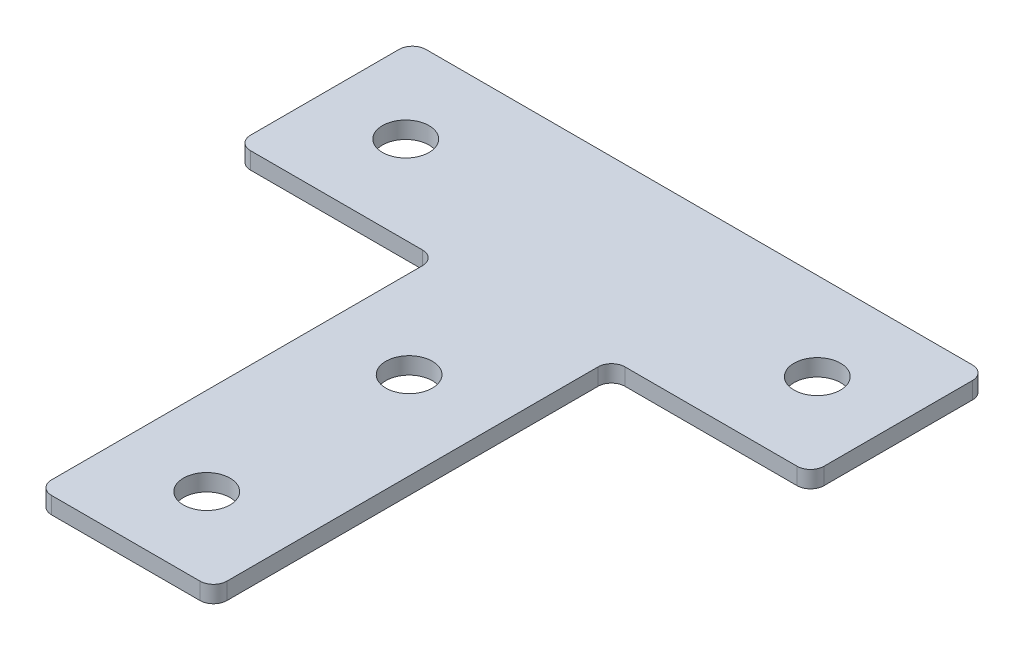
SolidWorks part; units mm, degrees
material "201 退火不锈钢 (SS)"
ref_plane "前视基准面" through (0, 0, 0) normal (0, 0, 1) x (1, 0, 0)
ref_plane "上视基准面" through (0, 0, 0) normal (0, 1, 0) x (1, 0, 0)
ref_plane "右视基准面" through (0, 0, 0) normal (1, 0, 0) x (0, 0, -1)
sketch "草图1" plane through (0, 0, 0) normal (0, 1, 0) x (1, 0, 0)
  line L0 (13, -13) -> (42.5, -13)
  line L1 (-42.5, 13) -> (42.5, 13)
  line L2 (-42.5, 13) -> (-42.5, -13)
  line L3 (-42.5, -13) -> (-13, -13)
  line L4 (42.5, 13) -> (42.5, -13)
  line L5 (-42.5, 13) -> (42.5, -13) construction
  line L6 (-42.5, -13) -> (42.5, 13) construction
  line L7 (-13, -72) -> (13, -72)
  line L8 (-13, -72) -> (-13, -13)
  line L10 (13, -72) -> (13, -13)
  line L11 (-13, -72) -> (13, -13) construction
  line L12 (-13, -13) -> (13, -72) construction
  circle A0 centre (0, -60) radius 3.45
  circle A1 centre (0, -30) radius 3.45
  circle A2 centre (-30.5, 0) radius 3.45
  circle A3 centre (30.5, 0) radius 3.45
  point P0 (0, 0)
  point P6 (0, -42.5)
  dimension "D6" = 6.9
  dimension "D7" = 12
  dimension "D8" = 30
  dimension "D9" = 12
  dimension "D10" = 12
  dimension "D1" = 85
  dimension "D2" = 85
  dimension "D3" = 26
  dimension "D4" = 26
  dimension "D5" = 0
extrude "凸台-拉伸1" add sketch "草图1" along normal blind 2.5
fillet "圆角1" radius 2 8 edges at (13, 1.25, 72) (-13, 1.25, 72) (-13, 1.25, 13) (-42.5, 1.25, 13) (13, 1.25, 13) (42.5, 1.25, 13) (42.5, 1.25, -13) (-42.5, 1.25, -13)
